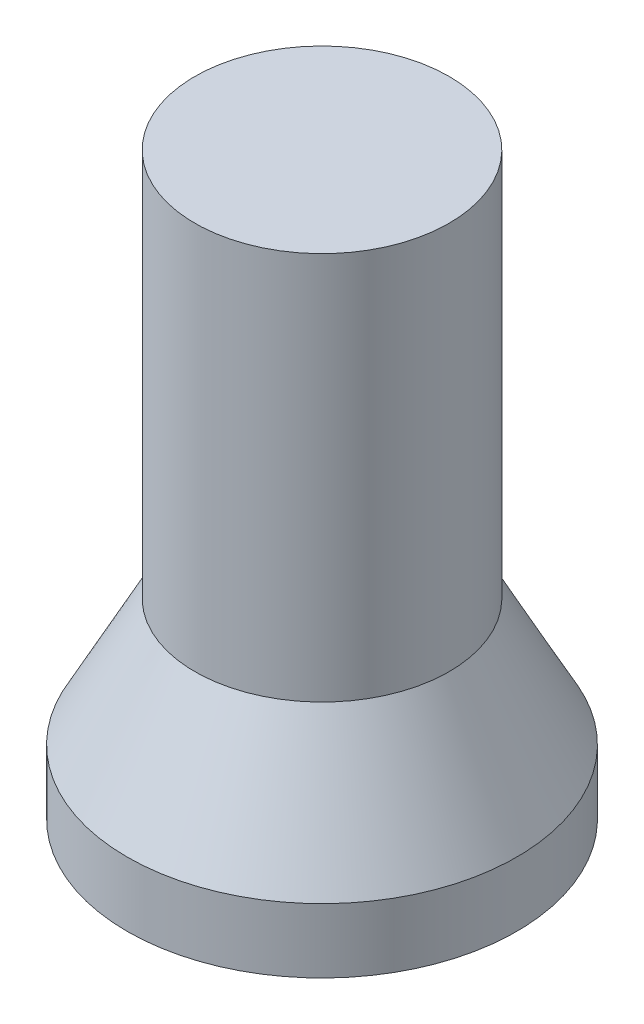
SolidWorks part; units mm, degrees
material "ABS"
ref_plane "Front Plane" through (0, 0, 0) normal (0, 0, 1) x (1, 0, 0)
ref_plane "Top Plane" through (0, 0, 0) normal (0, 1, 0) x (1, 0, 0)
ref_plane "Right Plane" through (0, 0, 0) normal (1, 0, 0) x (0, 0, -1)
sketch "Sketch3" plane through (0, 0, 0) normal (1, 0, 0) x (0, 0, -1)
  line L4 (5.05, 0) -> (5.05, 2)
  line L5 (5.05, 0) -> (6.05, 0)
  line L6 (0, 3.5) -> (5.25, 3.5) construction
  line L8 (6.05, 2) -> (3.95, 5.9375)
  line L11 (4.5167, 3) -> (5.05, 2)
  line L13 (0, 18) -> (3.95, 18)
  line L14 (3.95, 18) -> (3.95, 5.9375)
  line L15 (0, 3) -> (0, 18)
  line L16 (4.5167, 3) -> (0, 3)
  line L18 (6.05, 2) -> (6.05, 0)
  point P5 (4.506, 3)
  point P6 (0, 0)
  dimension "D1" = 18
  dimension "D2" = 1
  dimension "D4" = 2
  dimension "D5" = 5.05
  dimension "D6" = 3.95
  dimension "D7" = 3.5
  dimension "D8" = 1
  dimension "D9" = 5.25
ref_axis "Axis1" through (0, -43.5149, 0) along (0, 1, 0)
revolve "Revolve3" add sketch "Sketch3" angle 360 about axis through (0, -43.5149, 0) along (0, 1, 0)
